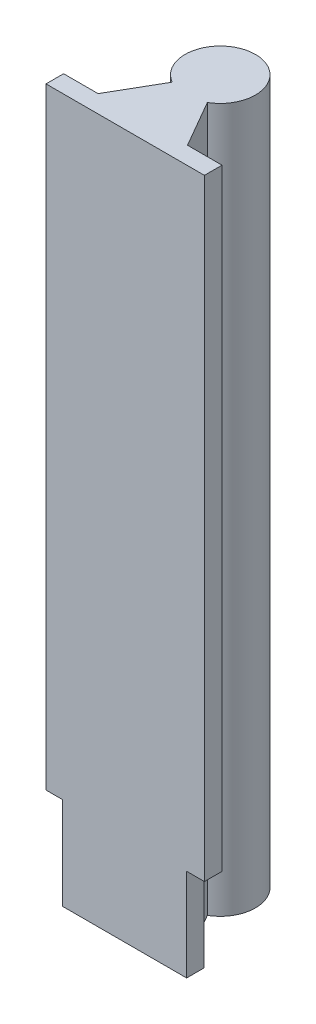
SolidWorks part; units mm, degrees
ref_plane "Front Plane" through (0, 0, 0) normal (0, 0, 1) x (1, 0, 0)
ref_plane "Top Plane" through (0, 0, 0) normal (0, 1, 0) x (1, 0, 0)
ref_plane "Right Plane" through (0, 0, 0) normal (1, 0, 0) x (0, 0, -1)
sketch "Sketch1" plane through (0, 0, 0) normal (0, 1, 0) x (1, 0, 0)
  line L0 (0, 24.5) -> (0, 0) construction
  line L1 (22.5, -2.5) -> (-22.5, -2.5)
  line L2 (22.5, -2.5) -> (22.5, 2.5)
  line L3 (22.5, 2.5) -> (12.7017, 2.5)
  line L4 (-22.5, -2.5) -> (-22.5, 2.5)
  line L5 (22.5, -2.5) -> (-22.5, 2.5) construction
  line L6 (22.5, 2.5) -> (-22.5, -2.5) construction
  line L7 (-5, 15.8397) -> (-12.7017, 2.5)
  line L8 (5, 15.8397) -> (12.7017, 2.5)
  line L9 (-12.7017, 2.5) -> (-22.5, 2.5)
  arc A0 (5, 15.8397) -> (-5, 15.8397) centre (0, 24.5) ccw
  point P0 (0, 0)
  dimension "D1" = 20
  dimension "D2" = 27
  dimension "D3" = 45
  dimension "D4" = 5
  dimension "D5" = 30
  dimension "D6" = 30
extrude "Boss-Extrude1" add sketch "Sketch1" along normal blind 200
sketch "Sketch2" plane through (0, 0, -2.5) normal (0, 0, -1) x (-1, 0, 0)
  line L0 (22.5, 200) -> (22.5, 0) construction
  line L1 (27.1159, -2.6814) -> (17.8841, -2.6814)
  line L2 (27.1159, -2.6814) -> (27.1159, 26.2549)
  line L3 (27.1159, 26.2549) -> (17.8841, 26.2549)
  line L4 (17.8841, -2.6814) -> (17.8841, 26.2549)
  line L5 (27.1159, -2.6814) -> (17.8841, 26.2549) construction
  line L6 (27.1159, 26.2549) -> (17.8841, -2.6814) construction
  line L7 (-22.5, 200) -> (-22.5, 0) construction
  line L8 (-27.5464, -2.6814) -> (-17.4536, -2.6814)
  line L9 (-27.5464, -2.6814) -> (-27.5464, 26.2549)
  line L10 (-27.5464, 26.2549) -> (-17.4536, 26.2549)
  line L11 (-17.4536, -2.6814) -> (-17.4536, 26.2549)
  line L12 (-27.5464, -2.6814) -> (-17.4536, 26.2549) construction
  line L13 (-27.5464, 26.2549) -> (-17.4536, -2.6814) construction
  point P0 (22.5, 11.7867)
  point P7 (-22.5, 11.7867)
extrude "Cut-Extrude1" cut sketch "Sketch2" against normal through all
